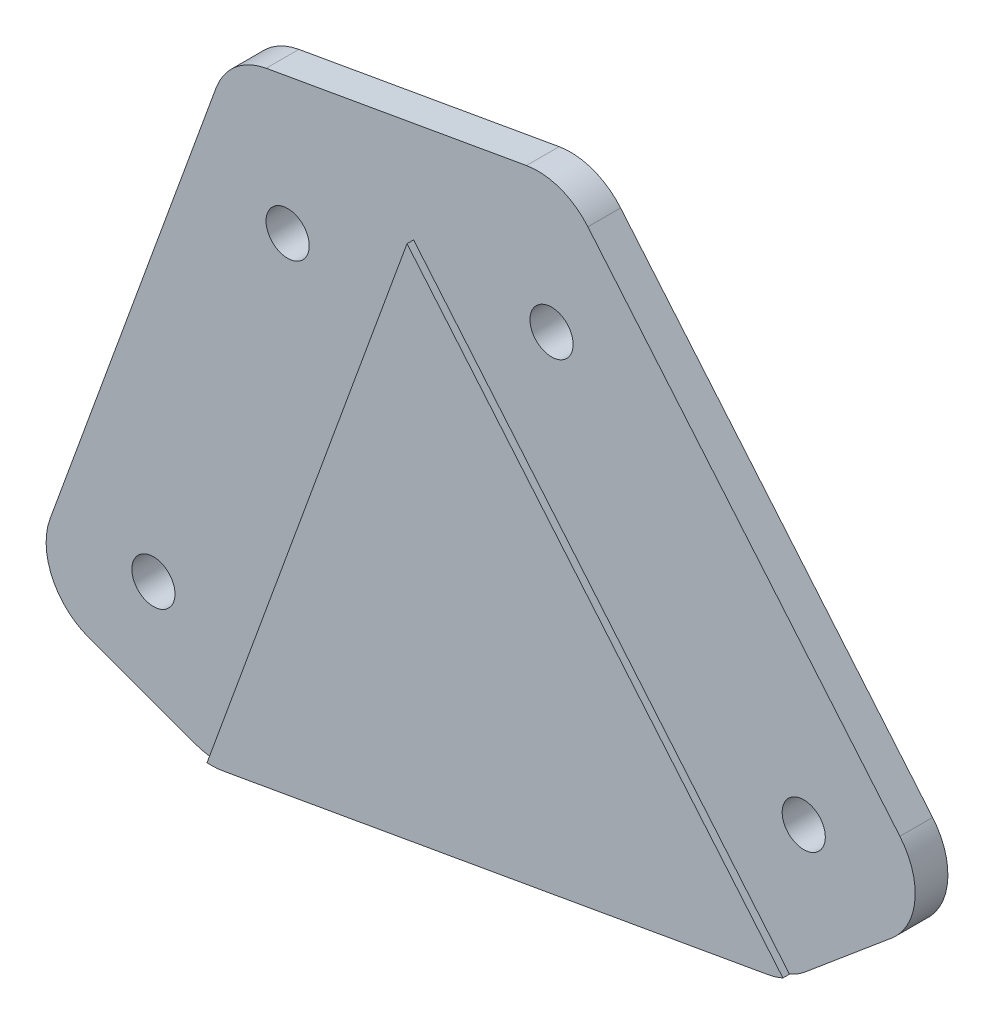
SolidWorks part; units mm, degrees
material "3.1325 (EN-AW 2017A)"
ref_plane "正面" through (0, 0, 0) normal (0, 0, 1) x (1, 0, 0)
ref_plane "平面" through (0, 0, 0) normal (0, 1, 0) x (1, 0, 0)
ref_plane "右側面" through (0, 0, 0) normal (1, 0, 0) x (0, 0, -1)
sketch "ｽｹｯﾁ1" plane through (0, 0, 0) normal (0, 0, 1) x (1, 0, 0)
  line L0 (0, 0) -> (133.1152, 365.731) construction
  line L1 (133.1152, 365.731) -> (440, 0) construction
  line L2 (440, 0) -> (0, 0) construction
  line L3 (133.1152, 365.731) -> (133.1152, 0) construction
  line L13 (133.1152, 365.731) -> (119.0198, 370.8613)
  line L14 (119.0198, 370.8613) -> (103.6289, 328.5752)
  line L15 (103.6289, 328.5752) -> (117.7243, 323.4449)
  line L16 (117.7243, 323.4449) -> (162.0407, 331.259)
  line L17 (162.0407, 331.259) -> (173.5313, 340.9009)
  line L18 (173.5313, 340.9009) -> (144.6059, 375.3729)
  line L19 (144.6059, 375.3729) -> (133.1152, 365.731)
  line L20 (144.6059, 375.3729) -> (119.0198, 370.8613)
  dimension "D4" = 15
  dimension "D5" = 15
  dimension "D6" = 45
  dimension "D1" = 440
  dimension "D2" = 70
  dimension "D3" = 50
  dimension "D7" = 45
extrude "ﾎﾞｽ - 押し出し1" add sketch "ｽｹｯﾁ1" along normal blind 3 contours L18 L19 L13 L14 L15 L16 L17 | L19 L20 L13
sketch "ｽｹｯﾁ2" plane through (0, 0, 3) normal (0, 0, 1) x (1, 0, 0)
  line L0 (103.6289, 328.5752) -> (117.7243, 323.4449) construction
  line L1 (119.0198, 370.8613) -> (103.6289, 328.5752) construction
  line L2 (173.5313, 340.9009) -> (144.6059, 375.3729) construction
  line L3 (162.0407, 331.259) -> (173.5313, 340.9009) construction
  circle A0 centre (113.2418, 333.0577) radius 1.65
  circle A1 centre (123.5024, 361.2485) radius 1.65
  circle A2 centre (143.6815, 364.8066) radius 1.65
  circle A3 centre (162.9651, 341.8253) radius 1.65
  dimension "D2" = 3.3
  dimension "D3" = 7.5
  dimension "D4" = 3.3
  dimension "D5" = 7.5
  dimension "D6" = 7.5
  dimension "D7" = 3.3
  dimension "D9" = 7.5
  dimension "D10" = 3.3
  dimension "D11" = 30
  dimension "D12" = 30
  dimension "D1" = 7.5
  dimension "D8" = 7.5
extrude "ｶｯﾄ - 押し出し1" cut sketch "ｽｹｯﾁ2" against normal blind 3
fillet "ﾌｨﾚｯﾄ1" radius 5 6 edges at (144.6059, 375.3729, 1.5) (119.0198, 370.8613, 1.5) (173.5313, 340.9009, 1.5) (162.0407, 331.259, 1.5) (117.7243, 323.4449, 1.5) (103.6289, 328.5752, 1.5)
sketch "ｽｹｯﾁ3" plane through (0, 0, 3) normal (0, 0, 1) x (1, 0, 0)
  line L0 (121.414, 377.4392) -> (103.6289, 328.5752)
  line L1 (121.414, 377.4392) -> (131.7116, 373.6912)
  line L2 (103.6289, 328.5752) -> (117.7713, 323.4278)
  line L3 (133.1326, 365.6326) -> (117.7713, 323.4278)
  line L4 (118.0325, 368.1487) -> (105.339, 333.2736) construction
  line L5 (140.1064, 380.7352) -> (173.5313, 340.9009)
  line L6 (140.1064, 380.7352) -> (131.7116, 373.6912)
  line L7 (173.5313, 340.9009) -> (162.0024, 331.2269)
  line L8 (133.1326, 365.6326) -> (162.0024, 331.2269)
  line L9 (170.3174, 344.7311) -> (146.4614, 373.1615) construction
  line L10 (108.3274, 326.8651) -> (116.4654, 323.9031) construction
  line L11 (163.067, 332.1202) -> (169.7011, 337.6869) construction
  line L12 (131.7116, 373.6912) -> (135.5563, 372.2918) construction
  line L13 (135.5563, 372.2918) -> (133.1326, 365.6326) construction
  line L14 (128.5774, 371.0612) -> (133.1326, 365.6326) construction
  line L15 (131.7116, 373.6912) -> (128.5774, 371.0612) construction
  dimension "D1" = 15.05
  dimension "D2" = 15.05
  dimension "D3" = 52
  dimension "D4" = 52
extrude "ｶｯﾄ - 押し出し2" cut sketch "ｽｹｯﾁ3" against normal blind 0.5
